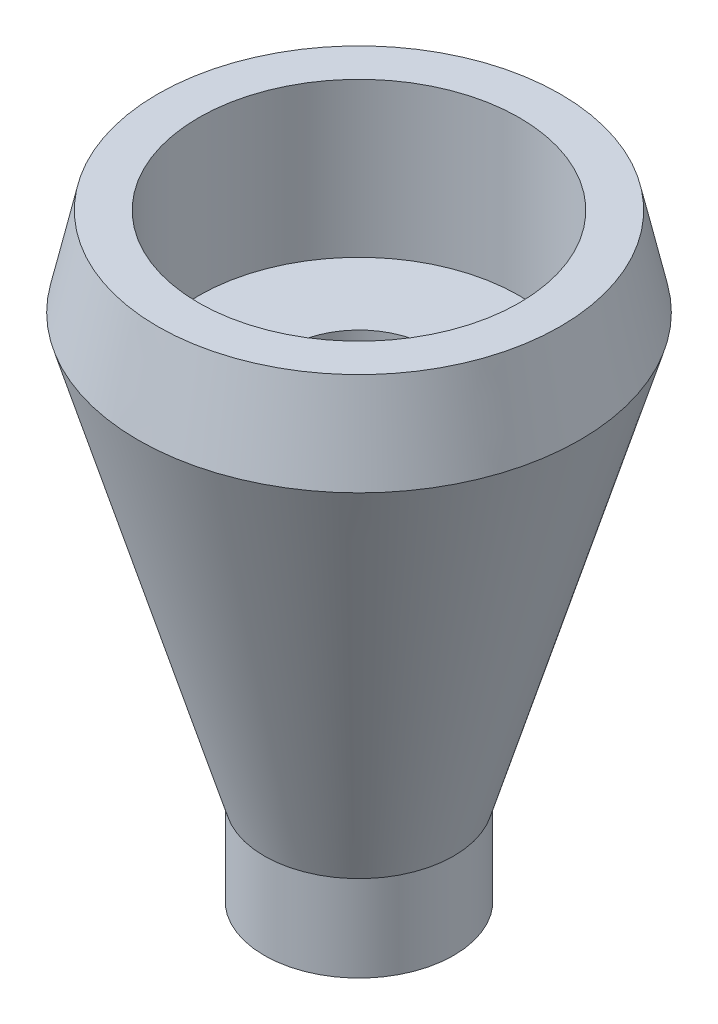
SolidWorks part; units mm, degrees
ref_plane "Front Plane" through (0, 0, 0) normal (0, 0, 1) x (1, 0, 0)
ref_plane "Top Plane" through (0, 0, 0) normal (0, 1, 0) x (1, 0, 0)
ref_plane "Right Plane" through (0, 0, 0) normal (1, 0, 0) x (0, 0, -1)
sketch "Sketch1" plane through (0, 0, 0) normal (0, 0, 1) x (1, 0, 0)
  line L0 (0, 0) -> (0, 6.4621)
  line L1 (-1.754, 6.4621) -> (-7.1083, 6.4621)
  line L2 (-7.1083, 6.4621) -> (-7.1083, 0)
  line L3 (-7.1083, 0) -> (0, 0)
  line L6 (9.4624, 38.2189) -> (0, 6.4621)
  line L9 (7.9965, 44.8657) -> (9.4624, 38.2189)
  line L10 (4.926, 33.2993) -> (-1.754, 33.2993)
  line L11 (-1.754, 33.2993) -> (-1.754, 6.4621)
  line L12 (7.9965, 44.8657) -> (4.926, 44.8657)
  line L13 (4.926, 44.8657) -> (4.926, 33.2993)
revolve "Revolve1" add sketch "Sketch1" angle 360 about L2
